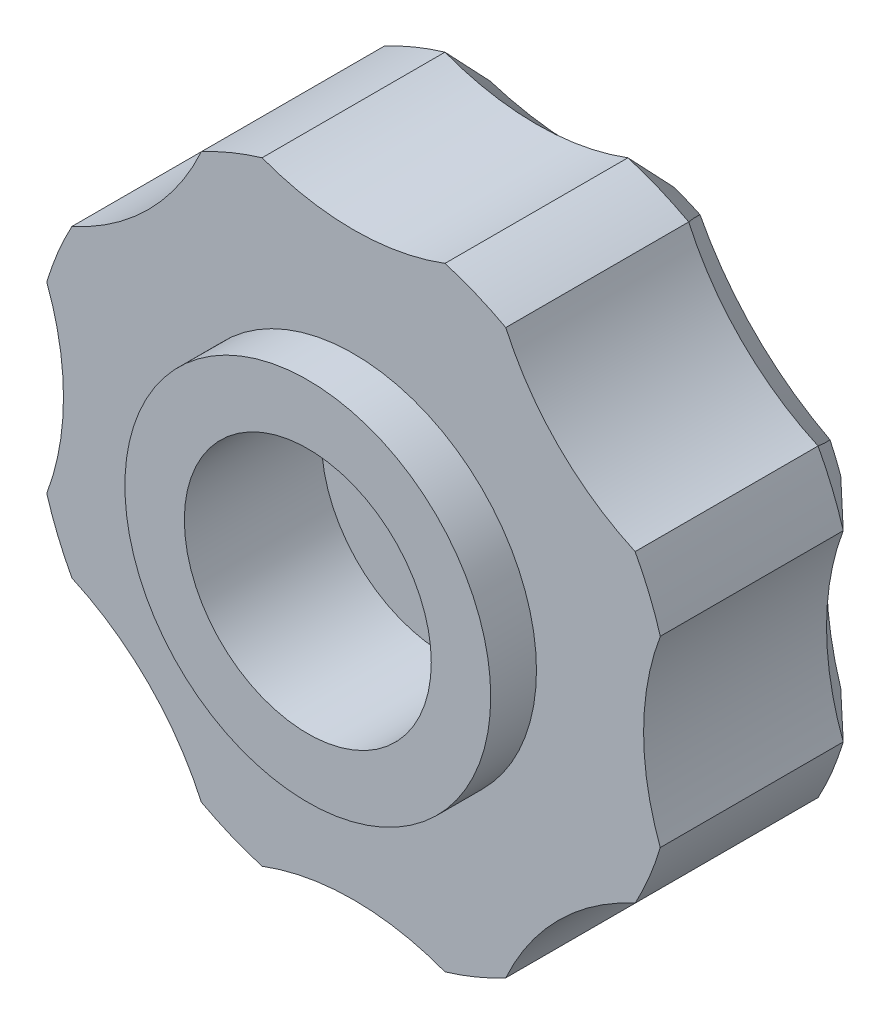
SolidWorks part; units mm, degrees
ref_plane "Plan de face" through (0, 0, 0) normal (0, 0, 1) x (1, 0, 0)
ref_plane "Plan de dessus" through (0, 0, 0) normal (0, 1, 0) x (1, 0, 0)
ref_plane "Plan de droite" through (0, 0, 0) normal (1, 0, 0) x (0, 0, -1)
sketch "Esquisse1" plane through (0, 0, 0) normal (0, 0, 1) x (1, 0, 0)
  circle A0 centre (0, 0) radius 7
  dimension "D1" = 14
extrude "Boss.-Extru.1" add sketch "Esquisse1" along normal blind 5
sketch "Esquisse2" plane through (0, 0, 5) normal (0, 0, 1) x (1, 0, 0)
  line L0 (0, 0) -> (0, 12) construction
  arc A0 (2, 6.7082) -> (-2, 6.7082) centre (0, 12) cw
  circle A1 centre (0, 0) radius 7 construction
  arc A2 (-2, 6.7082) -> (2, 6.7082) centre (0, 0) cw
  circle M2 centre (0, 0) radius 7
  dimension "D1" = 2
  dimension "D2" = 12
extrude "Enlèv. mat.-Extru.2" cut sketch "Esquisse2" against normal through all contours L0 A0 M2 | A0 L0 A2
pattern_circular "Répétition circulaire1" count 8 every 45 about axis through (0, 0, 0) along (0, 0, 1) of "Enlèv. mat.-Extru.2"
chamfer "Chanfrein1" distance 1 angle 45 16 edges at (-6.4672, 2.6788, 0) (-6.4672, -2.6788, 0) (-4.4851, -4.4851, 0) (-2.6788, -6.4672, 0) (0, -6.3429, 0) (2.6788, -6.4672, 0) (4.4851, -4.4851, 0) (6.4672, -2.6788, 0) (6.3429, 0, 0) (6.4672, 2.6788, 0) (4.4851, 4.4851, 0) (2.6788, 6.4672, 0) (0, 6.3429, 0) (-2.6788, 6.4672, 0) (-4.4851, 4.4851, 0) (-6.3429, 0, 0)
sketch "Esquisse3" plane through (0, 0, 5) normal (0, 0, 1) x (1, 0, 0)
  circle A0 centre (0, 0) radius 4
  dimension "D1" = 8
extrude "Boss.-Extru.2" add sketch "Esquisse3" along normal blind 1
sketch "Esquisse4" plane through (0, 0, 6) normal (0, 0, 1) x (1, 0, 0)
  circle A0 centre (0, 0) radius 2.7
  dimension "D1" = 5.4
extrude "Enlèv. mat.-Extru.3" cut sketch "Esquisse4" against normal blind 3
